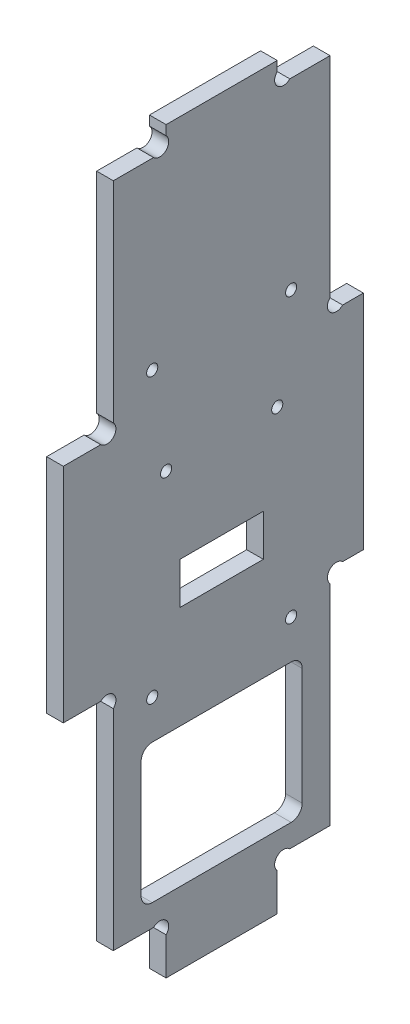
SolidWorks part; units mm, degrees
ref_plane "Plan de face" through (0, 0, 0) normal (0, 0, 1) x (1, 0, 0)
ref_plane "Plan de dessus" through (0, 0, 0) normal (0, 1, 0) x (1, 0, 0)
ref_plane "Plan de droite" through (0, 0, 0) normal (1, 0, 0) x (0, 0, -1)
sketch "Esquisse1" plane through (0, 0, 0) normal (1, 0, 0) x (0, 0, -1)
  line L13 (18.5, 6.7373) -> (18.5, 0)
  line L15 (16.2373, 9) -> (9, 9)
  line L17 (50.2627, 49) -> (54, 49)
  line L18 (6.7373, 49) -> (0, 49)
  line L19 (38.5, 6.7373) -> (38.5, 0)
  line L20 (50.2627, 89) -> (54, 89)
  line L21 (6.7373, 89) -> (0, 89)
  line L22 (18.5, 0) -> (38.5, 0)
  line L23 (40.7627, 9) -> (48, 9)
  line L24 (48, 9) -> (48, 46.7373)
  line L25 (9, 9) -> (9, 46.7373)
  line L26 (54, 89) -> (54, 49)
  line L27 (0, 49) -> (0, 89)
  line L29 (18.5, 131.2627) -> (18.5, 133)
  line L30 (38.5, 131.2627) -> (38.5, 133)
  line L31 (9, 91.2627) -> (9, 129)
  line L32 (9, 129) -> (16.2373, 129)
  line L33 (18.5, 133) -> (38.5, 133)
  line L34 (40.7627, 129) -> (48, 129)
  line L35 (48, 129) -> (48, 91.2627)
  arc A0 (50.2627, 49) -> (48, 46.7373) centre (49.1314, 47.8686) ccw
  arc A1 (9, 46.7373) -> (6.7373, 49) centre (7.8686, 47.8686) ccw
  arc A2 (18.5, 6.7373) -> (16.2373, 9) centre (17.3686, 7.8686) ccw
  arc A3 (38.5, 6.7373) -> (40.7627, 9) centre (39.6314, 7.8686) cw
  arc A4 (9, 91.2627) -> (6.7373, 89) centre (7.8686, 90.1314) cw
  arc A5 (50.2627, 89) -> (48, 91.2627) centre (49.1314, 90.1314) cw
  arc A6 (16.2373, 129) -> (18.5, 131.2627) centre (17.3686, 130.1314) ccw
  arc A7 (40.7627, 129) -> (38.5, 131.2627) centre (39.6314, 130.1314) cw
  point P1 (12.6186, 9)
  dimension "D14" = 1.1314
  dimension "D15" = 1.1314
  dimension "D17" = 1.1314
  dimension "D23" = 1.1314
  dimension "D10" = 1.6
  dimension "D1" = 6
  dimension "D2" = 9
  dimension "D3" = 9.5
  dimension "D4" = 9.5
  dimension "D5" = 9
  dimension "D6" = 40
  dimension "D7" = 40
  dimension "D8" = 40
  dimension "D9" = 4
  dimension "D11" = 1.1314
  dimension "D12" = 1.1314
  dimension "D13" = 1.1314
  dimension "D16" = 20
  dimension "D18" = 1.1314
  dimension "D19" = 1.1314
  dimension "D20" = 1.1314
  dimension "D21" = 1.1314
  dimension "D22" = 1.1314
  dimension "D24" = 3.7373
  dimension "D25" = 1.7373
  dimension "D26" = 1.1314
  dimension "D27" = 7.2373
  dimension "D28" = 1.1314
  dimension "D29" = 1.7373
  dimension "D30" = 20
  dimension "D31" = 39
  dimension "D32" = 39
extrude "Extrusion1" add sketch "Esquisse1" along normal blind 3
sketch "Esquisse2" plane through (0, 0, 0) normal (-1, 0, 0) x (0, 0, 1)
  line L0 (-48, 9) -> (-48, 46.7373) construction
  line L1 (-9, 9) -> (-16.2373, 9) construction
  line L2 (-9, 46.7373) -> (-9, 9) construction
  line L3 (-40.7627, 9) -> (-48, 9) construction
  line L4 (-14, 38) -> (-43, 38)
  line L5 (-14, 38) -> (-14, 13)
  line L6 (-14, 13) -> (-43, 13)
  line L7 (-43, 38) -> (-43, 13)
  line L8 (-48, 9) -> (-48, 46.7373) construction
  line L9 (-9, 46.7373) -> (-9, 9) construction
  circle A0 centre (-38.5, 79) radius 1
  circle A1 centre (-18.5, 79) radius 1
  dimension "D1" = 2
  dimension "D2" = 9.5
  dimension "D3" = 20
  dimension "D4" = 9.5
  dimension "D5" = 70
  dimension "D6" = 4
  dimension "D7" = 5
  dimension "D8" = 5
  dimension "D9" = 25
extrude "Enlèv. mat.-Extru.1" cut sketch "Esquisse2" against normal through all
fillet "Congé1" radius 2 4 edges at (1.5, 13, -43) (1.5, 13, -14) (1.5, 38, -14) (1.5, 38, -43)
sketch "Esquisse3" plane through (0, 0, 0) normal (-1, 0, 0) x (0, 0, 1)
  line L1 (-36, 64) -> (-21, 64)
  line L2 (-36, 64) -> (-36, 56.5)
  line L3 (-36, 56.5) -> (-21, 56.5)
  line L4 (-21, 64) -> (-21, 56.5)
  circle A0 centre (-38.5, 79) radius 1 construction
  circle A1 centre (-18.5, 79) radius 1 construction
  dimension "D1" = 15
  dimension "D2" = 7.5
  dimension "D3" = 2.5
  dimension "D4" = 2.5
  dimension "D5" = 15
extrude "Enlèv. mat.-Extru.2" cut sketch "Esquisse3" against normal through all
sketch "Esquisse4" plane through (0, 0, 0) normal (-1, 0, 0) x (0, 0, 1)
  line L0 (-36, 64) -> (-36, 56.5) construction
  line L1 (-21, 56.5) -> (-21, 64) construction
  line L2 (-14, 15) -> (-14, 36) construction
  line L3 (-16, 38) -> (-41, 38) construction
  line L4 (-43, 36) -> (-43, 15) construction
  line L5 (-36, 64) -> (-36, 56.5) construction
  circle A0 centre (-41, 96) radius 1
  circle A1 centre (-16, 96) radius 1
  circle A2 centre (-18.5, 79) radius 1 construction
  circle A3 centre (-41, 45) radius 1
  circle A4 centre (-16, 45) radius 1
  dimension "D1" = 2
  dimension "D2" = 5
  dimension "D3" = 5
  dimension "D4" = 17
  dimension "D5" = 7
  dimension "D6" = 2
  dimension "D7" = 2
  dimension "D8" = 5
extrude "Enlèv. mat.-Extru.3" cut sketch "Esquisse4" against normal through all
